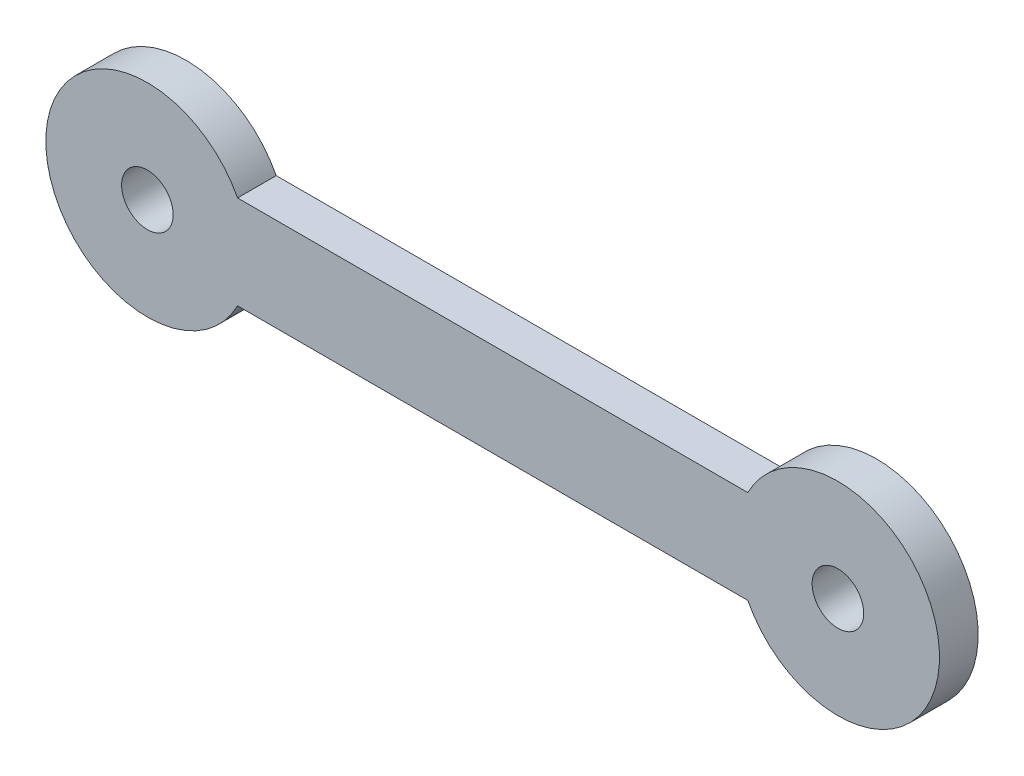
SolidWorks part; units mm, degrees
ref_plane "Front Plane" through (0, 0, 0) normal (0, 0, 1) x (1, 0, 0)
ref_plane "Top Plane" through (0, 0, 0) normal (0, 1, 0) x (1, 0, 0)
ref_plane "Right Plane" through (0, 0, 0) normal (1, 0, 0) x (0, 0, -1)
sketch "Sketch1" plane through (0, 0, 0) normal (0, 0, 1) x (1, 0, 0)
  line L0 (-1050.0024, 0) -> (-25.0012, 0) construction
  line L2 (22.1994, 11.4998) -> (147.8002, 11.4998)
  line L4 (22.1994, -11.4998) -> (147.8002, -11.4998)
  line L5 (25.0012, 0) -> (144.9984, 0) construction
  line L6 (169.9997, 0) -> (1216.6137, 0) construction
  arc A0 (22.1994, 11.4998) -> (22.1994, -11.4998) centre (0, 0) ccw
  arc A1 (147.8002, -11.4998) -> (147.8002, 11.4998) centre (169.9997, 0) ccw
  circle A2 centre (0, 0) radius 6.35
  circle A3 centre (169.9997, 0) radius 6.35
  dimension "D2" = 50.0024
  dimension "D4" = 12.7
  dimension "D1" = 169.9997
  dimension "D3" = 11.4998
extrude "Boss-Extrude1" add sketch "Sketch1" along normal blind 9.525
